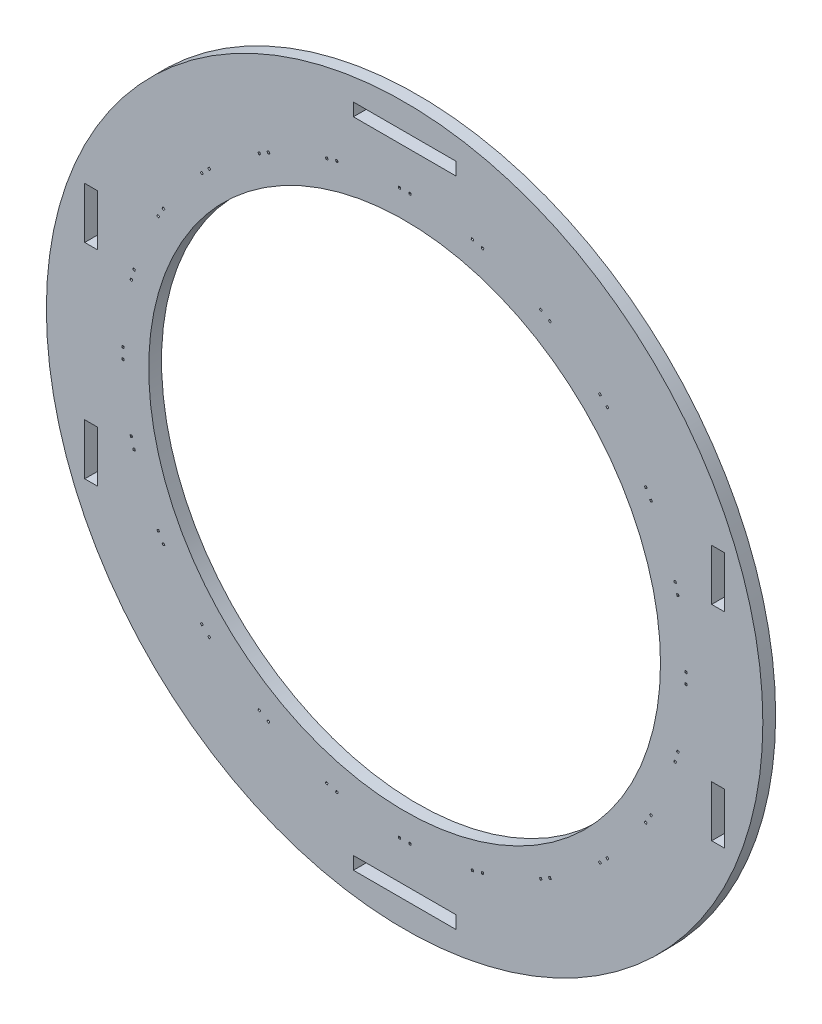
SolidWorks part; units mm, degrees
ref_plane "Front Plane" through (0, 0, 0) normal (0, 0, 1) x (1, 0, 0)
ref_plane "Top Plane" through (0, 0, 0) normal (0, 1, 0) x (1, 0, 0)
ref_plane "Right Plane" through (0, 0, 0) normal (1, 0, 0) x (0, 0, -1)
sketch "Sketch1" plane through (0, 0, 0) normal (0, 0, 1) x (1, 0, 0)
  line L0 (0, 63.5) -> (0, 69.85) construction
  line L1 (-1.3017, 69.85) -> (1.3017, 69.85) construction
  line L2 (1.5684, 69.5833) -> (1.035, 70.1167) construction
  line L3 (-1.5684, 70.1167) -> (-1.035, 70.1167)
  line L4 (-1.5684, 70.1167) -> (-1.5684, 69.5833)
  line L5 (-1.5684, 69.5833) -> (-1.035, 69.5833)
  line L6 (-1.035, 70.1167) -> (-1.035, 69.5833)
  line L7 (-1.5684, 70.1167) -> (-1.035, 69.5833) construction
  line L8 (-1.5684, 69.5833) -> (-1.035, 70.1167) construction
  line L9 (1.5684, 70.1167) -> (1.035, 69.5833) construction
  line L10 (1.035, 70.1167) -> (1.035, 69.5833)
  line L11 (1.5684, 69.5833) -> (1.035, 69.5833)
  line L12 (1.5684, 70.1167) -> (1.5684, 69.5833)
  line L13 (1.5684, 70.1167) -> (1.035, 70.1167)
  line L14 (16.6325, 68.1335) -> (17.1478, 67.9954)
  line L15 (16.6325, 68.1335) -> (16.4945, 67.6183)
  line L16 (16.4945, 67.6183) -> (17.0097, 67.4802)
  line L17 (17.1478, 67.9954) -> (17.0097, 67.4802)
  line L18 (19.1473, 67.4596) -> (19.0093, 66.9444)
  line L19 (19.5245, 66.8064) -> (19.0093, 66.9444)
  line L20 (19.6625, 67.3216) -> (19.5245, 66.8064)
  line L21 (19.6625, 67.3216) -> (19.1473, 67.4596)
  line L22 (19.5245, 66.8064) -> (19.1473, 67.4596) construction
  line L23 (16.6325, 68.1335) -> (17.0097, 67.4802) construction
  line L24 (16.4945, 67.6183) -> (17.1478, 67.9954) construction
  line L25 (19.6625, 67.3216) -> (19.0093, 66.9444) construction
  line L26 (33.7, 61.5071) -> (34.162, 61.2404)
  line L27 (33.7, 61.5071) -> (33.4333, 61.0451)
  line L28 (33.4333, 61.0451) -> (33.8953, 60.7784)
  line L29 (34.162, 61.2404) -> (33.8953, 60.7784)
  line L30 (35.9547, 60.2053) -> (35.688, 59.7434)
  line L31 (36.15, 59.4767) -> (35.688, 59.7434)
  line L32 (36.4167, 59.9386) -> (36.15, 59.4767)
  line L33 (36.4167, 59.9386) -> (35.9547, 60.2053)
  line L34 (36.15, 59.4767) -> (35.9547, 60.2053) construction
  line L35 (33.7, 61.5071) -> (33.8953, 60.7784) construction
  line L36 (33.4333, 61.0451) -> (34.162, 61.2404) construction
  line L37 (36.4167, 59.9386) -> (35.688, 59.7434) construction
  line L38 (48.4709, 50.6891) -> (48.8481, 50.3119)
  line L39 (48.4709, 50.6891) -> (48.0938, 50.3119)
  line L40 (48.0938, 50.3119) -> (48.4709, 49.9347)
  line L41 (48.8481, 50.3119) -> (48.4709, 49.9347)
  line L42 (50.3119, 48.8481) -> (49.9347, 48.4709)
  line L43 (50.3119, 48.0938) -> (49.9347, 48.4709)
  line L44 (50.6891, 48.4709) -> (50.3119, 48.0938)
  line L45 (50.6891, 48.4709) -> (50.3119, 48.8481)
  line L46 (50.3119, 48.0938) -> (50.3119, 48.8481) construction
  line L47 (48.4709, 50.6891) -> (48.4709, 49.9347) construction
  line L48 (48.0938, 50.3119) -> (48.8481, 50.3119) construction
  line L49 (50.6891, 48.4709) -> (49.9347, 48.4709) construction
  line L50 (59.9386, 36.4167) -> (60.2053, 35.9547)
  line L51 (59.9386, 36.4167) -> (59.4767, 36.15)
  line L52 (59.4767, 36.15) -> (59.7434, 35.688)
  line L53 (60.2053, 35.9547) -> (59.7434, 35.688)
  line L54 (61.2404, 34.162) -> (60.7784, 33.8953)
  line L55 (61.0451, 33.4333) -> (60.7784, 33.8953)
  line L56 (61.5071, 33.7) -> (61.0451, 33.4333)
  line L57 (61.5071, 33.7) -> (61.2404, 34.162)
  line L58 (61.0451, 33.4333) -> (61.2404, 34.162) construction
  line L59 (59.9386, 36.4167) -> (59.7434, 35.688) construction
  line L60 (59.4767, 36.15) -> (60.2053, 35.9547) construction
  line L61 (61.5071, 33.7) -> (60.7784, 33.8953) construction
  line L62 (67.3216, 19.6625) -> (67.4596, 19.1473)
  line L63 (67.3216, 19.6625) -> (66.8064, 19.5245)
  line L64 (66.8064, 19.5245) -> (66.9444, 19.0093)
  line L65 (67.4596, 19.1473) -> (66.9444, 19.0093)
  line L66 (67.9954, 17.1478) -> (67.4802, 17.0097)
  line L67 (67.6183, 16.4945) -> (67.4802, 17.0097)
  line L68 (68.1335, 16.6325) -> (67.6183, 16.4945)
  line L69 (68.1335, 16.6325) -> (67.9954, 17.1478)
  line L70 (67.6183, 16.4945) -> (67.9954, 17.1478) construction
  line L71 (67.3216, 19.6625) -> (66.9444, 19.0093) construction
  line L72 (66.8064, 19.5245) -> (67.4596, 19.1473) construction
  line L73 (68.1335, 16.6325) -> (67.4802, 17.0097) construction
  line L74 (70.1167, 1.5685) -> (70.1167, 1.0351)
  line L75 (70.1167, 1.5685) -> (69.5833, 1.5685)
  line L76 (69.5833, 1.5685) -> (69.5833, 1.0351)
  line L77 (70.1167, 1.0351) -> (69.5833, 1.0351)
  line L78 (70.1167, -1.035) -> (69.5833, -1.035)
  line L79 (69.5833, -1.5684) -> (69.5833, -1.035)
  line L80 (70.1167, -1.5684) -> (69.5833, -1.5684)
  line L81 (70.1167, -1.5684) -> (70.1167, -1.035)
  line L82 (69.5833, -1.5684) -> (70.1167, -1.035) construction
  line L83 (70.1167, 1.5685) -> (69.5833, 1.0351) construction
  line L84 (69.5833, 1.5685) -> (70.1167, 1.0351) construction
  line L85 (70.1167, -1.5684) -> (69.5833, -1.035) construction
  line L86 (68.1335, -16.6325) -> (67.9954, -17.1478)
  line L87 (68.1335, -16.6325) -> (67.6183, -16.4945)
  line L88 (67.6183, -16.4945) -> (67.4802, -17.0097)
  line L89 (67.9954, -17.1478) -> (67.4802, -17.0097)
  line L90 (67.4596, -19.1473) -> (66.9444, -19.0093)
  line L91 (66.8064, -19.5245) -> (66.9444, -19.0093)
  line L92 (67.3216, -19.6625) -> (66.8064, -19.5245)
  line L93 (67.3216, -19.6625) -> (67.4596, -19.1473)
  line L94 (66.8064, -19.5245) -> (67.4596, -19.1473) construction
  line L95 (68.1335, -16.6325) -> (67.4802, -17.0097) construction
  line L96 (67.6183, -16.4945) -> (67.9954, -17.1478) construction
  line L97 (67.3216, -19.6625) -> (66.9444, -19.0093) construction
  line L98 (61.5071, -33.7) -> (61.2404, -34.162)
  line L99 (61.5071, -33.7) -> (61.0451, -33.4333)
  line L100 (61.0451, -33.4333) -> (60.7784, -33.8953)
  line L101 (61.2404, -34.162) -> (60.7784, -33.8953)
  line L102 (60.2053, -35.9547) -> (59.7434, -35.688)
  line L103 (59.4767, -36.15) -> (59.7434, -35.688)
  line L104 (59.9386, -36.4167) -> (59.4767, -36.15)
  line L105 (59.9386, -36.4167) -> (60.2053, -35.9547)
  line L106 (59.4767, -36.15) -> (60.2053, -35.9547) construction
  line L107 (61.5071, -33.7) -> (60.7784, -33.8953) construction
  line L108 (61.0451, -33.4333) -> (61.2404, -34.162) construction
  line L109 (59.9386, -36.4167) -> (59.7434, -35.688) construction
  line L110 (50.6891, -48.4709) -> (50.3119, -48.8481)
  line L111 (50.6891, -48.4709) -> (50.3119, -48.0938)
  line L112 (50.3119, -48.0938) -> (49.9347, -48.4709)
  line L113 (50.3119, -48.8481) -> (49.9347, -48.4709)
  line L114 (48.8481, -50.3119) -> (48.4709, -49.9347)
  line L115 (48.0938, -50.3119) -> (48.4709, -49.9347)
  line L116 (48.4709, -50.6891) -> (48.0938, -50.3119)
  line L117 (48.4709, -50.6891) -> (48.8481, -50.3119)
  line L118 (48.0938, -50.3119) -> (48.8481, -50.3119) construction
  line L119 (50.6891, -48.4709) -> (49.9347, -48.4709) construction
  line L120 (50.3119, -48.0938) -> (50.3119, -48.8481) construction
  line L121 (48.4709, -50.6891) -> (48.4709, -49.9347) construction
  line L122 (36.4167, -59.9386) -> (35.9547, -60.2053)
  line L123 (36.4167, -59.9386) -> (36.15, -59.4767)
  line L124 (36.15, -59.4767) -> (35.688, -59.7434)
  line L125 (35.9547, -60.2053) -> (35.688, -59.7434)
  line L126 (34.162, -61.2404) -> (33.8953, -60.7784)
  line L127 (33.4333, -61.0451) -> (33.8953, -60.7784)
  line L128 (33.7, -61.5071) -> (33.4333, -61.0451)
  line L129 (33.7, -61.5071) -> (34.162, -61.2404)
  line L130 (33.4333, -61.0451) -> (34.162, -61.2404) construction
  line L131 (36.4167, -59.9386) -> (35.688, -59.7434) construction
  line L132 (36.15, -59.4767) -> (35.9547, -60.2053) construction
  line L133 (33.7, -61.5071) -> (33.8953, -60.7784) construction
  line L134 (19.6625, -67.3216) -> (19.1473, -67.4596)
  line L135 (19.6625, -67.3216) -> (19.5245, -66.8064)
  line L136 (19.5245, -66.8064) -> (19.0093, -66.9444)
  line L137 (19.1473, -67.4596) -> (19.0093, -66.9444)
  line L138 (17.1478, -67.9954) -> (17.0097, -67.4802)
  line L139 (16.4945, -67.6183) -> (17.0097, -67.4802)
  line L140 (16.6325, -68.1335) -> (16.4945, -67.6183)
  line L141 (16.6325, -68.1335) -> (17.1478, -67.9954)
  line L142 (16.4945, -67.6183) -> (17.1478, -67.9954) construction
  line L143 (19.6625, -67.3216) -> (19.0093, -66.9444) construction
  line L144 (19.5245, -66.8064) -> (19.1473, -67.4596) construction
  line L145 (16.6325, -68.1335) -> (17.0097, -67.4802) construction
  line L146 (1.5685, -70.1167) -> (1.0351, -70.1167)
  line L147 (1.5685, -70.1167) -> (1.5685, -69.5833)
  line L148 (1.5685, -69.5833) -> (1.0351, -69.5833)
  line L149 (1.0351, -70.1167) -> (1.0351, -69.5833)
  line L150 (-1.035, -70.1167) -> (-1.035, -69.5833)
  line L151 (-1.5684, -69.5833) -> (-1.035, -69.5833)
  line L152 (-1.5684, -70.1167) -> (-1.5684, -69.5833)
  line L153 (-1.5684, -70.1167) -> (-1.035, -70.1167)
  line L154 (-1.5684, -69.5833) -> (-1.035, -70.1167) construction
  line L155 (1.5685, -70.1167) -> (1.0351, -69.5833) construction
  line L156 (1.5685, -69.5833) -> (1.0351, -70.1167) construction
  line L157 (-1.5684, -70.1167) -> (-1.035, -69.5833) construction
  line L158 (-16.6325, -68.1335) -> (-17.1478, -67.9954)
  line L159 (-16.6325, -68.1335) -> (-16.4945, -67.6183)
  line L160 (-16.4945, -67.6183) -> (-17.0097, -67.4802)
  line L161 (-17.1478, -67.9954) -> (-17.0097, -67.4802)
  line L162 (-19.1473, -67.4596) -> (-19.0093, -66.9444)
  line L163 (-19.5245, -66.8064) -> (-19.0093, -66.9444)
  line L164 (-19.6625, -67.3216) -> (-19.5245, -66.8064)
  line L165 (-19.6625, -67.3216) -> (-19.1473, -67.4596)
  line L166 (-19.5245, -66.8064) -> (-19.1473, -67.4596) construction
  line L167 (-16.6325, -68.1335) -> (-17.0097, -67.4802) construction
  line L168 (-16.4945, -67.6183) -> (-17.1478, -67.9954) construction
  line L169 (-19.6625, -67.3216) -> (-19.0093, -66.9444) construction
  line L170 (-33.7, -61.5071) -> (-34.162, -61.2404)
  line L171 (-33.7, -61.5071) -> (-33.4333, -61.0451)
  line L172 (-33.4333, -61.0451) -> (-33.8953, -60.7784)
  line L173 (-34.162, -61.2404) -> (-33.8953, -60.7784)
  line L174 (-35.9547, -60.2053) -> (-35.688, -59.7434)
  line L175 (-36.15, -59.4767) -> (-35.688, -59.7434)
  line L176 (-36.4167, -59.9386) -> (-36.15, -59.4767)
  line L177 (-36.4167, -59.9386) -> (-35.9547, -60.2053)
  line L178 (-36.15, -59.4767) -> (-35.9547, -60.2053) construction
  line L179 (-33.7, -61.5071) -> (-33.8953, -60.7784) construction
  line L180 (-33.4333, -61.0451) -> (-34.162, -61.2404) construction
  line L181 (-36.4167, -59.9386) -> (-35.688, -59.7434) construction
  line L182 (-48.4709, -50.6891) -> (-48.8481, -50.3119)
  line L183 (-48.4709, -50.6891) -> (-48.0938, -50.3119)
  line L184 (-48.0938, -50.3119) -> (-48.4709, -49.9347)
  line L185 (-48.8481, -50.3119) -> (-48.4709, -49.9347)
  line L186 (-50.3119, -48.8481) -> (-49.9347, -48.4709)
  line L187 (-50.3119, -48.0938) -> (-49.9347, -48.4709)
  line L188 (-50.6891, -48.4709) -> (-50.3119, -48.0938)
  line L189 (-50.6891, -48.4709) -> (-50.3119, -48.8481)
  line L190 (-50.3119, -48.0938) -> (-50.3119, -48.8481) construction
  line L191 (-48.4709, -50.6891) -> (-48.4709, -49.9347) construction
  line L192 (-48.0938, -50.3119) -> (-48.8481, -50.3119) construction
  line L193 (-50.6891, -48.4709) -> (-49.9347, -48.4709) construction
  line L194 (-59.9386, -36.4167) -> (-60.2053, -35.9547)
  line L195 (-59.9386, -36.4167) -> (-59.4767, -36.15)
  line L196 (-59.4767, -36.15) -> (-59.7434, -35.688)
  line L197 (-60.2053, -35.9547) -> (-59.7434, -35.688)
  line L198 (-61.2404, -34.162) -> (-60.7784, -33.8953)
  line L199 (-61.0451, -33.4333) -> (-60.7784, -33.8953)
  line L200 (-61.5071, -33.7) -> (-61.0451, -33.4333)
  line L201 (-61.5071, -33.7) -> (-61.2404, -34.162)
  line L202 (-61.0451, -33.4333) -> (-61.2404, -34.162) construction
  line L203 (-59.9386, -36.4167) -> (-59.7434, -35.688) construction
  line L204 (-59.4767, -36.15) -> (-60.2053, -35.9547) construction
  line L205 (-61.5071, -33.7) -> (-60.7784, -33.8953) construction
  line L206 (-67.3216, -19.6625) -> (-67.4596, -19.1473)
  line L207 (-67.3216, -19.6625) -> (-66.8064, -19.5245)
  line L208 (-66.8064, -19.5245) -> (-66.9444, -19.0093)
  line L209 (-67.4596, -19.1473) -> (-66.9444, -19.0093)
  line L210 (-67.9954, -17.1478) -> (-67.4802, -17.0097)
  line L211 (-67.6183, -16.4945) -> (-67.4802, -17.0097)
  line L212 (-68.1335, -16.6325) -> (-67.6183, -16.4945)
  line L213 (-68.1335, -16.6325) -> (-67.9954, -17.1478)
  line L214 (-67.6183, -16.4945) -> (-67.9954, -17.1478) construction
  line L215 (-67.3216, -19.6625) -> (-66.9444, -19.0093) construction
  line L216 (-66.8064, -19.5245) -> (-67.4596, -19.1473) construction
  line L217 (-68.1335, -16.6325) -> (-67.4802, -17.0097) construction
  line L218 (-70.1167, -1.5685) -> (-70.1167, -1.0351)
  line L219 (-70.1167, -1.5685) -> (-69.5833, -1.5685)
  line L220 (-69.5833, -1.5685) -> (-69.5833, -1.0351)
  line L221 (-70.1167, -1.0351) -> (-69.5833, -1.0351)
  line L222 (-70.1167, 1.035) -> (-69.5833, 1.035)
  line L223 (-69.5833, 1.5684) -> (-69.5833, 1.035)
  line L224 (-70.1167, 1.5684) -> (-69.5833, 1.5684)
  line L225 (-70.1167, 1.5684) -> (-70.1167, 1.035)
  line L226 (-69.5833, 1.5684) -> (-70.1167, 1.035) construction
  line L227 (-70.1167, -1.5685) -> (-69.5833, -1.0351) construction
  line L228 (-69.5833, -1.5685) -> (-70.1167, -1.0351) construction
  line L229 (-70.1167, 1.5684) -> (-69.5833, 1.035) construction
  line L230 (-68.1335, 16.6325) -> (-67.9954, 17.1478)
  line L231 (-68.1335, 16.6325) -> (-67.6183, 16.4945)
  line L232 (-67.6183, 16.4945) -> (-67.4802, 17.0097)
  line L233 (-67.9954, 17.1478) -> (-67.4802, 17.0097)
  line L234 (-67.4596, 19.1473) -> (-66.9444, 19.0093)
  line L235 (-66.8064, 19.5245) -> (-66.9444, 19.0093)
  line L236 (-67.3216, 19.6625) -> (-66.8064, 19.5245)
  line L237 (-67.3216, 19.6625) -> (-67.4596, 19.1473)
  line L238 (-66.8064, 19.5245) -> (-67.4596, 19.1473) construction
  line L239 (-68.1335, 16.6325) -> (-67.4802, 17.0097) construction
  line L240 (-67.6183, 16.4945) -> (-67.9954, 17.1478) construction
  line L241 (-67.3216, 19.6625) -> (-66.9444, 19.0093) construction
  line L242 (-61.5071, 33.7) -> (-61.2404, 34.162)
  line L243 (-61.5071, 33.7) -> (-61.0451, 33.4333)
  line L244 (-61.0451, 33.4333) -> (-60.7784, 33.8953)
  line L245 (-61.2404, 34.162) -> (-60.7784, 33.8953)
  line L246 (-60.2053, 35.9547) -> (-59.7434, 35.688)
  line L247 (-59.4767, 36.15) -> (-59.7434, 35.688)
  line L248 (-59.9386, 36.4167) -> (-59.4767, 36.15)
  line L249 (-59.9386, 36.4167) -> (-60.2053, 35.9547)
  line L250 (-59.4767, 36.15) -> (-60.2053, 35.9547) construction
  line L251 (-61.5071, 33.7) -> (-60.7784, 33.8953) construction
  line L252 (-61.0451, 33.4333) -> (-61.2404, 34.162) construction
  line L253 (-59.9386, 36.4167) -> (-59.7434, 35.688) construction
  line L254 (-50.6891, 48.4709) -> (-50.3119, 48.8481)
  line L255 (-50.6891, 48.4709) -> (-50.3119, 48.0938)
  line L256 (-50.3119, 48.0938) -> (-49.9347, 48.4709)
  line L257 (-50.3119, 48.8481) -> (-49.9347, 48.4709)
  line L258 (-48.8481, 50.3119) -> (-48.4709, 49.9347)
  line L259 (-48.0938, 50.3119) -> (-48.4709, 49.9347)
  line L260 (-48.4709, 50.6891) -> (-48.0938, 50.3119)
  line L261 (-48.4709, 50.6891) -> (-48.8481, 50.3119)
  line L262 (-48.0938, 50.3119) -> (-48.8481, 50.3119) construction
  line L263 (-50.6891, 48.4709) -> (-49.9347, 48.4709) construction
  line L264 (-50.3119, 48.0938) -> (-50.3119, 48.8481) construction
  line L265 (-48.4709, 50.6891) -> (-48.4709, 49.9347) construction
  line L266 (-36.4167, 59.9386) -> (-35.9547, 60.2053)
  line L267 (-36.4167, 59.9386) -> (-36.15, 59.4767)
  line L268 (-36.15, 59.4767) -> (-35.688, 59.7434)
  line L269 (-35.9547, 60.2053) -> (-35.688, 59.7434)
  line L270 (-34.162, 61.2404) -> (-33.8953, 60.7784)
  line L271 (-33.4333, 61.0451) -> (-33.8953, 60.7784)
  line L272 (-33.7, 61.5071) -> (-33.4333, 61.0451)
  line L273 (-33.7, 61.5071) -> (-34.162, 61.2404)
  line L274 (-33.4333, 61.0451) -> (-34.162, 61.2404) construction
  line L275 (-36.4167, 59.9386) -> (-35.688, 59.7434) construction
  line L276 (-36.15, 59.4767) -> (-35.9547, 60.2053) construction
  line L277 (-33.7, 61.5071) -> (-33.8953, 60.7784) construction
  line L278 (-19.6625, 67.3216) -> (-19.1473, 67.4596)
  line L279 (-19.6625, 67.3216) -> (-19.5245, 66.8064)
  line L280 (-19.5245, 66.8064) -> (-19.0093, 66.9444)
  line L281 (-19.1473, 67.4596) -> (-19.0093, 66.9444)
  line L282 (-17.1478, 67.9954) -> (-17.0097, 67.4802)
  line L283 (-16.4945, 67.6183) -> (-17.0097, 67.4802)
  line L284 (-16.6325, 68.1335) -> (-16.4945, 67.6183)
  line L285 (-16.6325, 68.1335) -> (-17.1478, 67.9954)
  line L286 (-16.4945, 67.6183) -> (-17.1478, 67.9954) construction
  line L287 (-19.6625, 67.3216) -> (-19.0093, 66.9444) construction
  line L288 (-19.5245, 66.8064) -> (-19.1473, 67.4596) construction
  line L289 (-16.6325, 68.1335) -> (-17.0097, 67.4802) construction
  line L290 (76.2, 31.7348) -> (76.2, -31.7652) construction
  line L291 (76.2, -31.7652) -> (79.375, -31.7652) construction
  line L292 (79.375, -31.7652) -> (79.375, 31.7348) construction
  line L293 (79.375, 31.7348) -> (76.2, 31.7348) construction
  line L294 (0, -1000) -> (0, 49000) construction
  line L295 (76.2, 31.7348) -> (79.375, 31.7348)
  line L296 (76.2, 31.7348) -> (76.2, 19.0348)
  line L297 (76.2, 19.0348) -> (79.375, 19.0348)
  line L298 (79.375, 31.7348) -> (79.375, 19.0348)
  line L299 (76.2, -19.0652) -> (79.375, -19.0652)
  line L300 (76.2, -19.0652) -> (76.2, -31.7652)
  line L301 (76.2, -31.7652) -> (79.375, -31.7652)
  line L302 (79.375, -19.0652) -> (79.375, -31.7652)
  line L303 (-79.375, 31.7348) -> (-76.2, 31.7348) construction
  line L304 (-79.375, -31.7652) -> (-79.375, 31.7348) construction
  line L305 (-76.2, -31.7652) -> (-79.375, -31.7652) construction
  line L306 (-76.2, 31.7348) -> (-76.2, -31.7652) construction
  line L307 (-79.375, -19.0652) -> (-79.375, -31.7652)
  line L308 (-76.2, -31.7652) -> (-79.375, -31.7652)
  line L309 (-76.2, -19.0652) -> (-76.2, -31.7652)
  line L310 (-76.2, -19.0652) -> (-79.375, -19.0652)
  line L311 (-79.375, 31.7348) -> (-79.375, 19.0348)
  line L312 (-76.2, 19.0348) -> (-79.375, 19.0348)
  line L313 (-76.2, 31.7348) -> (-76.2, 19.0348)
  line L314 (-76.2, 31.7348) -> (-79.375, 31.7348)
  line L315 (-12.7, 79.375) -> (-12.7, 82.55)
  line L316 (-12.7, 79.375) -> (12.7, 79.375)
  line L317 (-12.7, 82.55) -> (12.7, 82.55)
  line L318 (12.7, 79.375) -> (12.7, 82.55)
  line L319 (-12.7, -79.375) -> (-12.7, -82.55)
  line L320 (-12.7, -79.375) -> (12.7, -79.375)
  line L321 (-12.7, -82.55) -> (12.7, -82.55)
  line L322 (12.7, -79.375) -> (12.7, -82.55)
  line L323 (12.7, -82.55) -> (12.7, -79.375) construction
  line L324 (12.7, 82.55) -> (12.7, 79.375) construction
  circle A0 centre (0, 0) radius 63.5
  circle A1 centre (0, 0) radius 88.9
  point P8 (0, 69.85)
  dimension "D1" = 127
  dimension "D2" = 177.8
  dimension "D5" = 0.5334
  dimension "D3" = 2.6035
  dimension "D4" = 6.35
  dimension "D6" = 76.2
  dimension "D7" = 3.175
  dimension "D8" = 63.5
  dimension "D9" = 31.7348
  dimension "D10" = 12.7
  dimension "D11" = 12.7
extrude "Boss-Extrude1" add sketch "Sketch1" along normal blind 3.175
